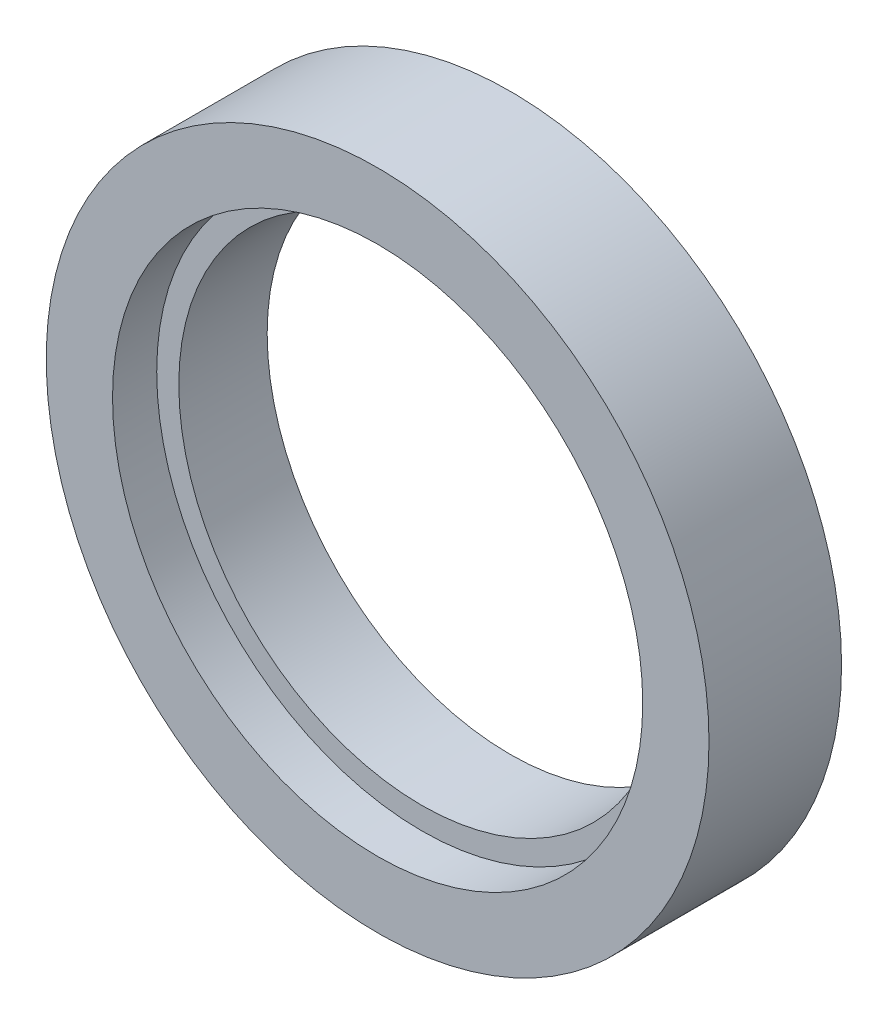
SolidWorks part; units mm, degrees
ref_plane "Plan de face" through (0, 0, 0) normal (0, 0, 1) x (1, 0, 0)
ref_plane "Plan de dessus" through (0, 0, 0) normal (0, 1, 0) x (1, 0, 0)
ref_plane "Plan de droite" through (0, 0, 0) normal (1, 0, 0) x (0, 0, -1)
sketch "Esquisse1" plane through (0, 0, 0) normal (0, 0, 1) x (1, 0, 0)
  circle A0 centre (0, 0) radius 7.5
  circle A1 centre (0, 0) radius 5.5
  dimension "D1" = 15
  dimension "D2" = 11
extrude "Boss.-Extru.1" add sketch "Esquisse1" along normal blind 3
sketch "Esquisse2" plane through (0, 0, 3) normal (0, 0, 1) x (1, 0, 0)
  circle A0 centre (0, 0) radius 6
  dimension "D1" = 12
extrude "Enlèv. mat.-Extru.1" cut sketch "Esquisse2" against normal blind 1
